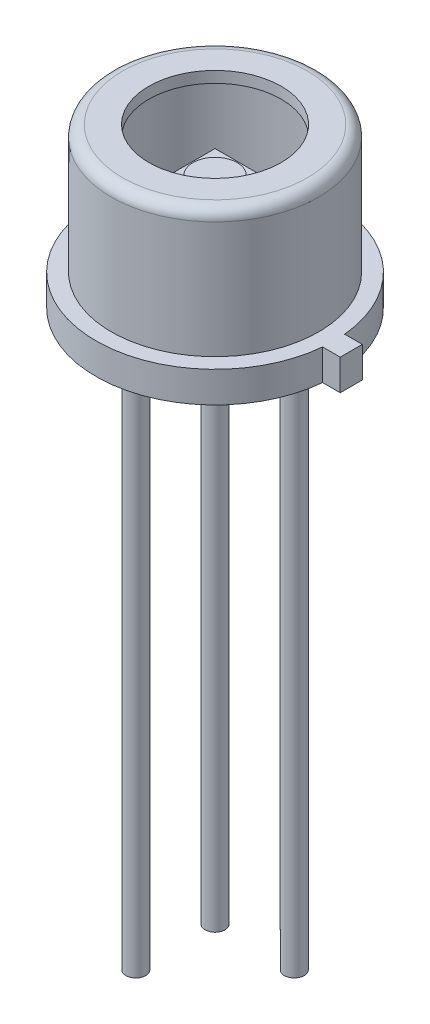
SolidWorks part; units mm, degrees
ref_plane "Front Plane" through (0, 0, 0) normal (0, 0, 1) x (1, 0, 0)
ref_plane "Top Plane" through (0, 0, 0) normal (0, 1, 0) x (1, 0, 0)
ref_plane "Right Plane" through (0, 0, 0) normal (1, 0, 0) x (0, 0, -1)
sketch "Sketch1" plane through (0, 0, 0) normal (0, 0, 1) x (1, 0, 0)
  line L0 (0, 0) -> (0, 37.7864) construction
  line L2 (2.7, 0) -> (2.7, 0.7)
  line L3 (2.7, 0.7) -> (2.35, 0.7)
  line L6 (2.35, 0.7) -> (2.35, 3.346)
  line L7 (2.096, 3.6) -> (1.5, 3.6)
  arc A0 (2.35, 3.346) -> (2.096, 3.6) centre (2.096, 3.346) ccw
  dimension "D7" = 0.254
  dimension "D1" = 0.7
  dimension "D2" = 4.7
  dimension "D4" = 5.4
  dimension "D6" = 3.6
  dimension "D8" = 3
revolve "Revolve-Thin2" add sketch "Sketch1" angle 360 about L0
sketch "Sketch2" plane through (0, 0, 0) normal (0, -1, 0) x (1, 0, 0)
  circle A1 centre (0, 0) radius 2.7
  circle A2 centre (0, 0) radius 2.7
  dimension "D1" = 0
extrude "Boss-Extrude1" add sketch "Sketch2" against normal up to surface (0.446 mm away) up to face at (0, 0.446, -2.096)
sketch "Sketch3" plane through (0, 0, 0) normal (0, -1, 0) x (1, 0, 0)
  line L0 (0.625, 0.625) -> (-0.625, -0.625) construction
  line L1 (-0.625, 0.625) -> (0.625, 0.625)
  line L2 (-0.625, 0.625) -> (-0.625, -0.625)
  line L3 (-0.625, -0.625) -> (0.625, -0.625)
  line L4 (0.625, 0.625) -> (0.625, -0.625)
  dimension "D1" = 1.25
extrude "Boss-Extrude2" add sketch "Sketch3" along normal blind 0.05 from offset 2.5 separate body offset against normal yes
sketch "Sketch8" plane through (0, 2.5, 0) normal (0, 1, 0) x (-1, 0, 0)
  circle A0 centre (0, 0) radius 0.5
  dimension "D1" = 1
extrude "Boss-Extrude6" add sketch "Sketch8" along normal blind 0.1 from surface at 0 starting at face at (0, 2.5, 0)
sketch "Sketch11" plane through (0, 0, 0) normal (0, -1, 0) x (1, 0, 0)
  line L0 (0, 0) -> (6.1157, 0) construction
  line L1 (3.0884, 0) -> (3.0884, -0.25)
  line L2 (3.0884, -0.25) -> (2.6884, -0.25)
  line L3 (3.0884, 0) -> (3.0884, 0.25)
  line L4 (3.0884, 0.25) -> (2.6884, 0.25)
  line L5 (0, 0) -> (0, 6.1969) construction
  circle A0 centre (0, 0) radius 4.57
  circle A1 centre (0, 0) radius 2.7 construction
  circle M1 centre (0, 0) radius 2.7
  dimension "D4" = 9.14
  dimension "D1" = 0.5
  dimension "D2" = 0.4
  dimension "D3" = 270
extrude "Boss-Extrude8" add sketch "Sketch11" against normal up to surface (0.7 mm away) contours L3 L4 L2 L1 M1 up to face at (0, 0.7, -2.35)
sketch "Sketch5" plane through (0, 0, 0) normal (0, -1, 0) x (1, 0, 0)
  line L0 (0, 0) -> (-0.898, 0.898) construction
  line L1 (0, 0) -> (1.27, 0) construction
  line L2 (0, 1.6552) -> (0, -1.2761) construction
  circle A0 centre (0, 0) radius 1.27 construction
  circle A2 centre (0.898, -0.898) radius 0.225
  circle A3 centre (-0.898, 0.898) radius 0.225
  circle A4 centre (-0.898, -0.898) radius 0.225
  circle A5 centre (0.898, 0.898) radius 0.225 [skipped]
  dimension "D1" = 2.54
  dimension "D2" = 135
  dimension "D3" = 4
  dimension "D5" = 0.45
extrude "Boss-Extrude4" add sketch "Sketch5" along normal blind 13
sketch "Sketch7" plane through (0, 0, 0) normal (0, -1, 0) x (1, 0, 0)
  circle A0 centre (-0.898, 0.898) radius 0.75
  dimension "D1" = 1.5
extrude "Boss-Extrude5" [suppressed] add sketch "Sketch7" along normal blind 0.4
sketch "Sketch9" plane through (0, 0, 0) normal (0, -1, 0) x (1, 0, 0)
  circle A0 centre (0, -3.8) radius 0.5
  dimension "D1" = 1
  dimension "D2" = 3.8
extrude "Boss-Extrude7" [suppressed] add sketch "Sketch9" along normal blind 0.01
